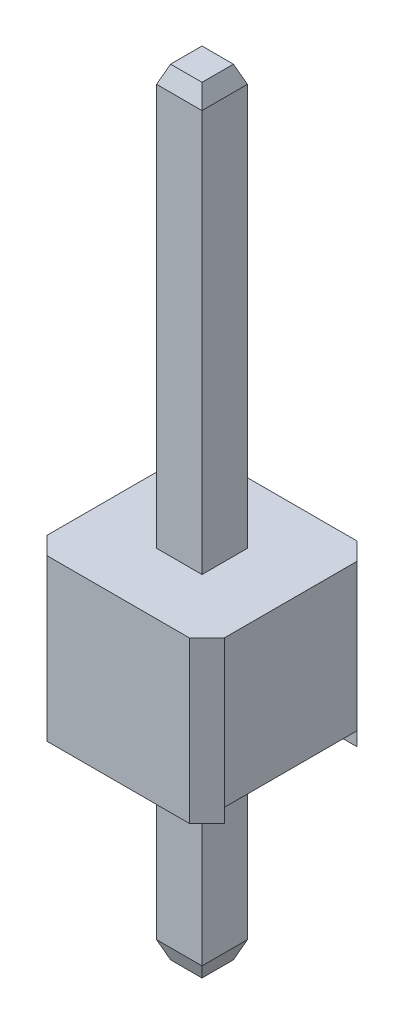
SolidWorks part; units mm, degrees
ref_plane "Front Plane" through (0, 0, 0) normal (0, 0, 1) x (1, 0, 0)
ref_plane "Top Plane" through (0, 0, 0) normal (0, 1, 0) x (1, 0, 0)
ref_plane "Right Plane" through (0, 0, 0) normal (1, 0, 0) x (0, 0, -1)
sketch "Sketch1" plane through (0, 0, 0) normal (0, 1, 0) x (1, 0, 0)
  line L1 (0, 0) -> (0.65, 0)
  line L2 (0, 0) -> (0, -0.65)
  line L3 (0, -0.65) -> (0.65, -0.65)
  line L4 (0.65, 0) -> (0.65, -0.65)
  dimension "D1" = 0.65
  dimension "D2" = 0.65
extrude "Boss-Extrude1" add sketch "Sketch1" along normal blind 11.3
chamfer "Chamfer1" distance 0.25 distance2 0.1 4 edges at (0.325, 11.3, 0) (0.65, 11.3, 0.325) (0.325, 11.3, 0.65) (0, 11.3, 0.325)
chamfer "Chamfer2" distance 0.1 distance2 0.25 4 edges at (0.325, 0, 0.65) (0.65, 0, 0.325) (0.325, 0, 0) (0, 0, 0.325)
ref_plane "Plane1" through (0, 3, 0) normal (0, -1, 0) x (-1, 0, 0)
sketch "Sketch2" plane through (0, 3, 0) normal (0, -1, 0) x (-1, 0, 0)
  line L0 (-0.65, -0.325) -> (0, -0.325) construction
  line L5 (-1.595, 0.875) -> (0.945, 0.875)
  line L6 (-1.595, 0.875) -> (-1.595, -1.525)
  line L7 (-1.595, -1.525) -> (0.945, -1.525)
  line L8 (0.945, 0.875) -> (0.945, -1.525)
  line L9 (-0.65, -0.65) -> (-0.65, 0) construction
  line L10 (0, 0) -> (0, -0.65) construction
  line L11 (-0.325, -0.325) -> (-2.865, -0.325) construction
  point P10 (-1.595, -0.325)
  point P13 (-1.595, -1.525)
  dimension "D1" = 2.4
  dimension "D2" = 1.2
  dimension "D3" = 2.54
  dimension "D4" = 1.27
extrude "Boss-Extrude2" add sketch "Sketch2" against normal blind 2.3
chamfer "Chamfer3" distance 0.25 angle 45 4 edges at (-0.945, 4.15, -0.875) (-0.945, 4.15, 1.525) (1.595, 4.15, 1.525) (1.595, 4.15, -0.875)
sketch "Sketch6" plane through (1.595, 0, 0) normal (1, 0, 0) x (0, 0, -1)
  line L0 (-1.527, 3) -> (1.527, 3) construction
  line L1 (-1.275, 3) -> (0.625, 3)
  line L2 (-1.275, 3) -> (-1.275, 3.2)
  line L3 (-1.275, 3.2) -> (0.625, 3.2)
  line L4 (0.625, 3) -> (0.625, 3.2)
  line L5 (-1.275, 5.3) -> (-1.275, 3) construction
  line L6 (0.625, 3) -> (0.625, 5.3) construction
  dimension "D1" = 0.2
extrude "Cut-Extrude5" cut sketch "Sketch6" against normal blind 6
sketch "Sketch7" plane through (0, 3.2, 0) normal (0, -1, 0) x (1, 0, 0)
  line L1 (0, 0) -> (0.65, 0)
  line L2 (0, 0) -> (0, 0.65)
  line L3 (0, 0.65) -> (0.65, 0.65)
  line L4 (0.65, 0) -> (0.65, 0.65)
extrude "Boss-Extrude4" add sketch "Sketch7" along normal blind 3
chamfer "Chamfer5" distance 0.25 distance2 0.1 4 edges at (0.325, 0.2, 0.65) (0.65, 0.2, 0.325) (0.325, 0.2, 0) (0, 0.2, 0.325)
